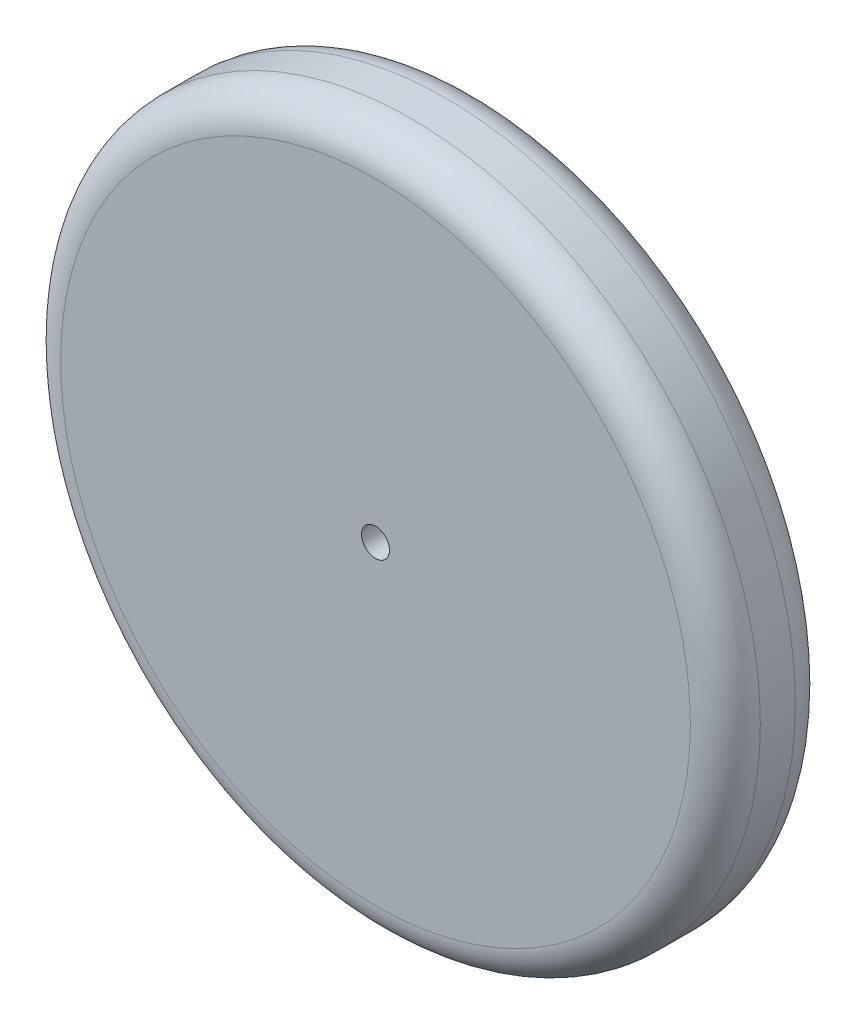
SolidWorks part; units mm, degrees
ref_plane "Alzado" through (0, 0, 0) normal (0, 0, 1) x (1, 0, 0)
ref_plane "Planta" through (0, 0, 0) normal (0, 1, 0) x (1, 0, 0)
ref_plane "Vista lateral" through (0, 0, 0) normal (1, 0, 0) x (0, 0, -1)
sketch "Croquis1" plane through (0, 0, 0) normal (0, 0, 1) x (1, 0, 0)
  circle A0 centre (0, 0) radius 4
  circle A1 centre (0, 0) radius 100
extrude "Saliente-Extruir1" add sketch "Croquis1" along normal blind 30
fillet "Redondeo1" radius 10 1 edges at (100, 0, 30)
fillet "Redondeo2" radius 10 1 edges at (100, 0, 0)
